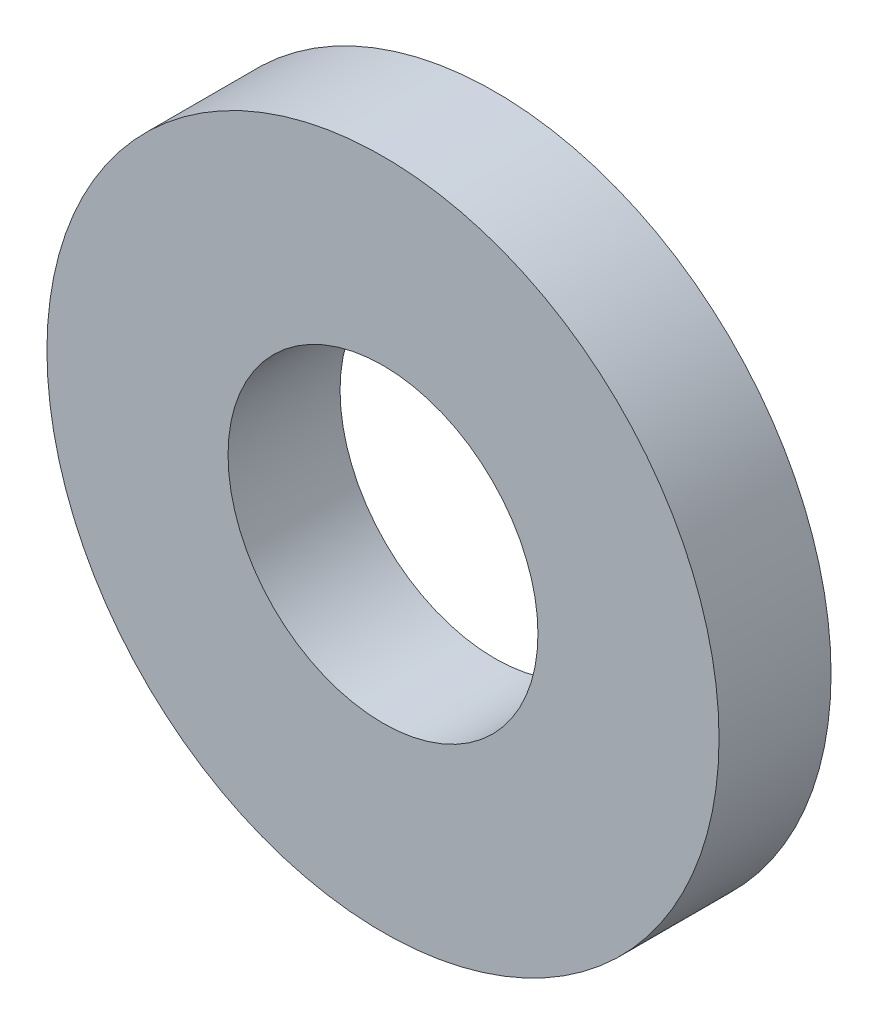
SolidWorks part; units mm, degrees
ref_plane "前视基准面" through (0, 0, 0) normal (0, 0, 1) x (1, 0, 0)
ref_plane "上视基准面" through (0, 0, 0) normal (0, 1, 0) x (1, 0, 0)
ref_plane "右视基准面" through (0, 0, 0) normal (1, 0, 0) x (0, 0, -1)
sketch "草图1" plane through (0, 0, 0) normal (0, 0, 1) x (1, 0, 0)
  circle A0 centre (0, 0) radius 9
  dimension "D1" = 18
extrude "凸台-拉伸1" add sketch "草图1" along normal blind 3
sketch "草图2" plane through (0, 0, 3) normal (0, 0, 1) x (1, 0, 0)
  circle A0 centre (0, 0) radius 4.15
  dimension "D1" = 8.3
extrude "切除-拉伸1" cut sketch "草图2" against normal through all
